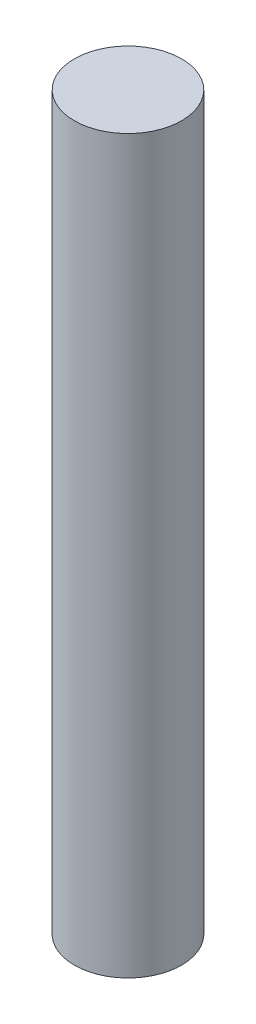
SolidWorks part; units mm, degrees
ref_plane "Front Plane" through (0, 0, 0) normal (0, 0, 1) x (1, 0, 0)
ref_plane "Top Plane" through (0, 0, 0) normal (0, 1, 0) x (1, 0, 0)
ref_plane "Right Plane" through (0, 0, 0) normal (1, 0, 0) x (0, 0, -1)
sketch "Sketch1" plane through (0, 0, 0) normal (0, 1, 0) x (1, 0, 0)
  circle A0 centre (0, 0) radius 1.1
  dimension "D1" = 2.2
extrude "Boss-Extrude2" add sketch "Sketch1" along normal blind 15 contours A0
